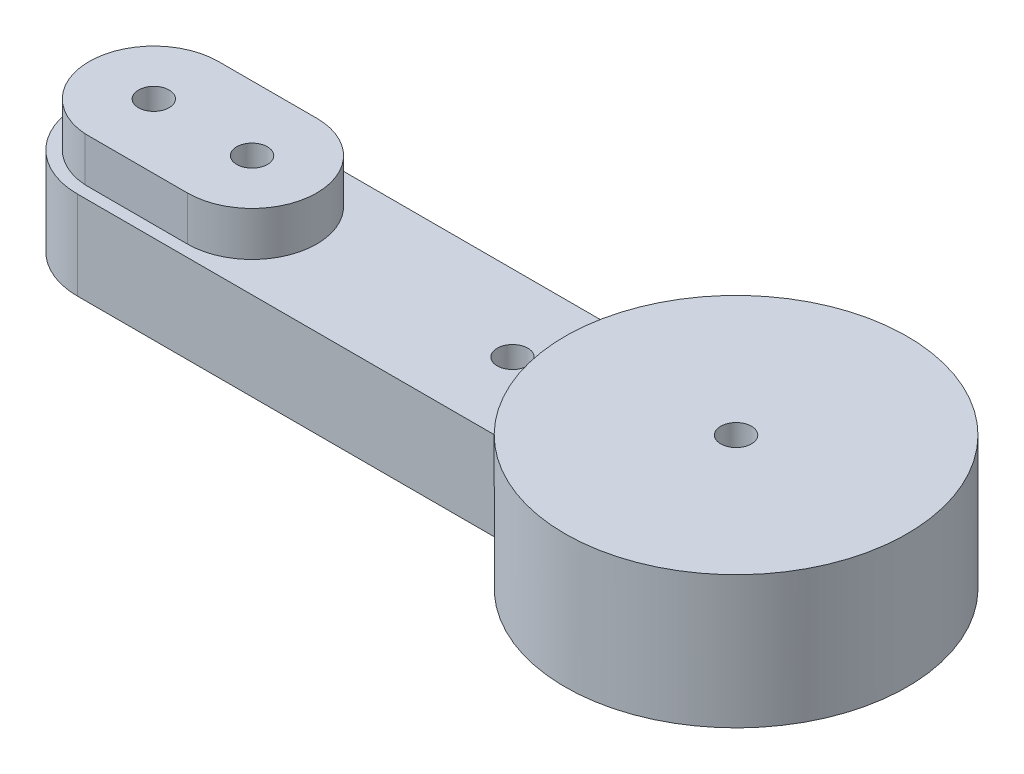
SolidWorks part; units mm, degrees
ref_plane "Front Plane" through (0, 0, 0) normal (0, 0, 1) x (1, 0, 0)
ref_plane "Top Plane" through (0, 0, 0) normal (0, 1, 0) x (1, 0, 0)
ref_plane "Right Plane" through (0, 0, 0) normal (1, 0, 0) x (0, 0, -1)
sketch "Sketch1" plane through (0, 0, 0) normal (0, 1, 0) x (1, 0, 0)
  line L0 (0, 0) -> (-23.7, 0) construction
  line L1 (-23.7, 3.108) -> (-6.2301, 3.108)
  line L2 (-23.7, -3.108) -> (-6.2301, -3.108)
  arc A0 (-6.2301, -3.108) -> (-6.2301, 3.108) centre (0, 0) ccw
  circle A1 centre (-23.7, 0) radius 0.625
  circle A2 centre (-19.7, 0) radius 0.625
  circle A3 centre (-9.1, 0) radius 0.625
  circle A4 centre (0, 0) radius 0.625
  arc A5 (-23.7, 3.108) -> (-23.7, -3.108) centre (-23.7, 0) ccw
  dimension "D1" = 23.7
  dimension "D4" = 1.25
  dimension "D2" = 4
  dimension "D3" = 14.6
extrude "Boss-Extrude1" add sketch "Sketch1" along normal blind 3.6
sketch "Sketch2" plane through (0, 3.6, 0) normal (0, 1, 0) x (1, 0, 0)
  line L0 (-19.7, 2.6338) -> (-23.7, 2.6338)
  line L1 (-19.7, -2.6338) -> (-23.8669, -2.6285)
  arc A0 (-23.7, 2.6338) -> (-23.5398, -2.6289) centre (-23.7, 0) ccw
  arc A1 (-19.7067, -2.6338) -> (-19.7, 2.6338) centre (-19.7, 0) ccw
  circle A2 centre (0, 0) radius 6.9623
  circle M4 centre (-23.7, 0) radius 0.625
  arc M7 (-6.2301, -3.108) -> (-6.2301, 3.108) centre (0, 0) ccw
  circle M9 centre (-19.7, 0) radius 0.625
  circle M10 centre (0, 0) radius 0.625
extrude "Boss-Extrude2" add sketch "Sketch2" along normal blind 1.8 contours L1 A1 L0 A0 M9 M4 | A2 M7 M10
